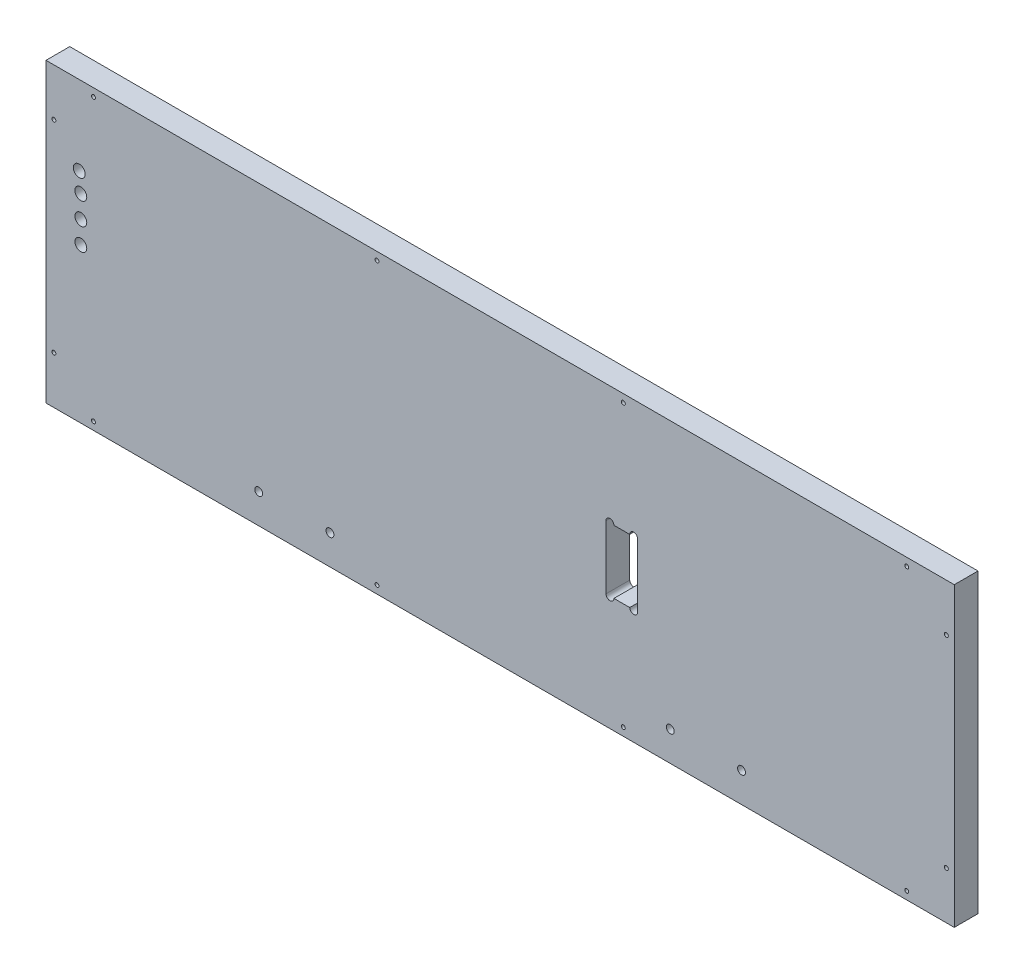
SolidWorks part; units mm, degrees
material "Pine"
ref_plane "Front Plane" through (0, 0, 0) normal (0, 0, 1) x (1, 0, 0)
ref_plane "Top Plane" through (0, 0, 0) normal (0, 1, 0) x (1, 0, 0)
ref_plane "Right Plane" through (0, 0, 0) normal (1, 0, 0) x (0, 0, -1)
sketch "Sketch1" plane through (0, 0, 0) normal (0, 0, 1) x (1, 0, 0)
  line L0 (-5300.6625, 1520.825) -> (-5451.475, 1520.825)
  line L1 (-5456.2375, 1384.3) -> (-5456.2375, 1516.0625)
  line L2 (-5557.8375, 1546.225) -> (-5194.3, 1546.225)
  line L3 (-5557.8375, 1539.875) -> (-5194.3, 1539.875)
  line L4 (-5297.4875, 1377.95) -> (-5454.65, 1377.95)
  line L5 (-5291.1375, 1384.3) -> (-5291.1375, 1516.0625)
  line L6 (-5300.6625, 1525.5875) -> (-5451.475, 1525.5875)
  line L7 (-5461, 1384.3) -> (-5461, 1516.0625)
  line L8 (-5297.4875, 1382.7125) -> (-5454.65, 1382.7125)
  line L9 (-5295.9, 1384.3) -> (-5295.9, 1516.0625)
  line L10 (-5740.4, 998.5375) -> (-5740.4, 1181.1)
  line L11 (-5740.4, 1181.1) -> (-5512.5938, 1181.1)
  line L12 (-5512.5938, 1181.1) -> (-5512.5938, 998.5375)
  line L13 (-5512.5938, 998.5375) -> (-5740.4, 998.5375)
  line L14 (-5258.5938, 1181.1) -> (-5486.4, 1181.1)
  line L15 (-5258.5938, 998.5375) -> (-5258.5938, 1181.1)
  line L16 (-5486.4, 998.5375) -> (-5258.5938, 998.5375)
  line L17 (-5486.4, 1181.1) -> (-5486.4, 998.5375)
  line L18 (-5740.4, 898.525) -> (-5011.7375, 898.525)
  line L19 (-5168.1062, 1384.3) -> (-5168.1062, 1392.2375)
  line L20 (-5176.0437, 1400.175) -> (-5245.8937, 1400.175)
  line L21 (-5253.8313, 1392.2375) -> (-5253.8313, 1384.3)
  line L22 (-5451.475, 1512.8875) -> (-5451.475, 1384.3)
  line L23 (-5303.8375, 1516.0625) -> (-5448.3, 1516.0625)
  line L24 (-5498.3062, 1384.3) -> (-5451.475, 1384.3)
  line L25 (-5253.8313, 1384.3) -> (-5300.6625, 1384.3)
  line L26 (-5584.0312, 1384.3) -> (-5740.4, 1384.3)
  line L27 (-5564.1875, 1536.7) -> (-5740.4, 1536.7)
  line L28 (-5740.4, 1357.3125) -> (-5740.4, 1206.5)
  line L29 (-5011.7375, 1357.3125) -> (-5740.4, 1357.3125)
  line L30 (-5011.7375, 1206.5) -> (-5011.7375, 1357.3125)
  line L31 (-5740.4, 1206.5) -> (-5011.7375, 1206.5)
  line L32 (-4765.675, 1549.4) -> (-4978.4, 1549.4)
  line L33 (-4765.675, 1397) -> (-4765.675, 1549.4)
  line L34 (-4978.4, 1397) -> (-4765.675, 1397)
  line L35 (-4978.4, 1549.4) -> (-4978.4, 1397)
  line L36 (-4765.675, 1371.6) -> (-4978.4, 1371.6)
  line L37 (-4765.675, 1219.2) -> (-4765.675, 1371.6)
  line L38 (-4978.4, 1219.2) -> (-4765.675, 1219.2)
  line L39 (-4978.4, 1371.6) -> (-4978.4, 1219.2)
  line L40 (-5284.7875, 803.275) -> (-5272.0875, 803.275)
  line L41 (-5187.95, 1536.7) -> (-5011.7375, 1536.7)
  line L42 (-5300.6625, 1384.3) -> (-5300.6625, 1512.8875)
  line L43 (-5740.4, 1536.7) -> (-5740.4, 1384.3)
  line L44 (-5557.8375, 1536.7) -> (-5557.8375, 1549.4)
  line L45 (-5557.8375, 1549.4) -> (-5194.3, 1549.4)
  line L46 (-5194.3, 1549.4) -> (-5194.3, 1536.7)
  line L47 (-5011.7375, 1536.7) -> (-5011.7375, 1384.3)
  line L48 (-5011.7375, 1384.3) -> (-5168.1062, 1384.3)
  line L49 (-5498.3062, 1384.3) -> (-5498.3062, 1392.2375)
  line L50 (-5506.2437, 1400.175) -> (-5576.0938, 1400.175)
  line L51 (-5584.0312, 1392.2375) -> (-5584.0312, 1384.3)
  line L52 (-5740.4, 660.4) -> (-5740.4, 898.525)
  line L53 (-5011.7375, 898.525) -> (-5011.7375, 660.4)
  line L54 (-5011.7375, 660.4) -> (-5740.4, 660.4)
  line L55 (-5291.1375, 803.275) -> (-5291.1375, 752.475)
  line L56 (-5265.7375, 752.475) -> (-5265.7375, 803.275)
  line L57 (-5284.7875, 752.475) -> (-5272.0875, 752.475)
  arc A0 (-5451.475, 1520.825) -> (-5456.2375, 1516.0625) centre (-5451.475, 1516.0625) ccw
  arc A1 (-5461, 1384.3) -> (-5454.65, 1377.95) centre (-5454.65, 1384.3) ccw
  arc A2 (-5297.4875, 1377.95) -> (-5291.1375, 1384.3) centre (-5297.4875, 1384.3) ccw
  circle A3 centre (-5037.9312, 1233.4875) radius 1.5875
  circle A4 centre (-5037.9312, 1328.7375) radius 1.5875
  circle A5 centre (-5714.2063, 1233.4875) radius 1.5875
  circle A6 centre (-5714.2063, 1328.7375) radius 1.5875
  circle A7 centre (-5018.0875, 1333.5) radius 1.5875
  circle A8 centre (-5018.0875, 1231.9) radius 1.5875
  circle A9 centre (-5734.05, 1231.9) radius 1.5875
  circle A10 centre (-5734.05, 1333.5) radius 1.5875
  circle A11 centre (-5734.05, 1511.3) radius 1.5875
  circle A12 centre (-5734.05, 1409.7) radius 1.5875
  circle A13 centre (-5018.0875, 1511.3) radius 1.5875
  circle A14 centre (-5018.0875, 1409.7) radius 1.5875
  arc A15 (-5557.8375, 1546.225) -> (-5557.8375, 1539.875) centre (-5557.8375, 1543.05) ccw
  arc A16 (-5194.3, 1539.875) -> (-5194.3, 1546.225) centre (-5194.3, 1543.05) ccw
  arc A17 (-5291.1375, 1516.0625) -> (-5300.6625, 1525.5875) centre (-5300.6625, 1516.0625) ccw
  arc A18 (-5451.475, 1525.5875) -> (-5461, 1516.0625) centre (-5451.475, 1516.0625) ccw
  arc A19 (-5456.2375, 1384.3) -> (-5454.65, 1382.7125) centre (-5454.65, 1384.3) ccw
  arc A20 (-5297.4875, 1382.7125) -> (-5295.9, 1384.3) centre (-5297.4875, 1384.3) ccw
  arc A21 (-5295.9, 1516.0625) -> (-5300.6625, 1520.825) centre (-5300.6625, 1516.0625) ccw
  circle A22 centre (-5702.3, 892.175) radius 1.5875
  circle A23 centre (-5734.05, 860.425) radius 1.5875
  circle A24 centre (-5474.8906, 892.175) radius 1.5875
  circle A25 centre (-5277.2469, 892.175) radius 1.5875
  circle A26 centre (-5049.8375, 892.175) radius 1.5875
  circle A27 centre (-5018.0875, 860.425) radius 1.5875
  circle A28 centre (-5296.6938, 1174.75) radius 1.5875
  circle A29 centre (-5448.3, 1174.75) radius 1.5875
  circle A30 centre (-5264.9437, 1155.7) radius 1.5875
  circle A31 centre (-5264.9437, 1023.9375) radius 1.5875
  circle A32 centre (-5518.9438, 1155.7) radius 1.5875
  circle A33 centre (-5518.9438, 1023.9375) radius 1.5875
  circle A34 centre (-5702.3, 1004.8875) radius 1.5875
  circle A35 centre (-5550.6937, 1004.8875) radius 1.5875
  arc A36 (-5576.0938, 1400.175) -> (-5584.0312, 1392.2375) centre (-5576.0938, 1392.2375) ccw
  arc A37 (-5168.1062, 1392.2375) -> (-5176.0437, 1400.175) centre (-5176.0437, 1392.2375) ccw
  arc A38 (-5245.8937, 1400.175) -> (-5253.8313, 1392.2375) centre (-5245.8937, 1392.2375) ccw
  arc A39 (-5448.3, 1516.0625) -> (-5451.475, 1512.8875) centre (-5448.3, 1512.8875) ccw
  arc A40 (-5284.7875, 803.275) -> (-5291.1375, 803.275) centre (-5287.9625, 803.275) ccw
  circle A41 centre (-5679.2812, 1026.3187) radius 1.5875
  circle A42 centre (-5679.2812, 1153.3187) radius 1.5875
  circle A43 centre (-5571.3313, 1153.3187) radius 1.5875
  circle A44 centre (-5571.3313, 1026.3187) radius 1.5875
  circle A45 centre (-5317.3312, 1153.3187) radius 1.5875
  circle A46 centre (-5317.3312, 1026.3187) radius 1.5875
  circle A47 centre (-5425.2812, 1026.3187) radius 1.5875
  circle A48 centre (-5425.2812, 1153.3187) radius 1.5875
  arc A49 (-5194.3, 1536.7) -> (-5187.95, 1536.7) centre (-5191.125, 1536.7) ccw
  arc A50 (-5564.1875, 1536.7) -> (-5557.8375, 1536.7) centre (-5561.0125, 1536.7) ccw
  arc A51 (-5300.6625, 1512.8875) -> (-5303.8375, 1516.0625) centre (-5303.8375, 1512.8875) ccw
  arc A52 (-5498.3062, 1392.2375) -> (-5506.2437, 1400.175) centre (-5506.2437, 1392.2375) ccw
  circle A53 centre (-5712.46, 784.225) radius 4.7625
  arc A54 (-5272.0875, 752.475) -> (-5265.7375, 752.475) centre (-5268.9125, 752.475) ccw
  arc A55 (-5291.1375, 752.475) -> (-5284.7875, 752.475) centre (-5287.9625, 752.475) ccw
  circle A56 centre (-5182.3938, 684.2125) radius 3.175
  circle A57 centre (-5239.5437, 684.2125) radius 3.175
  circle A58 centre (-5512.5938, 684.2125) radius 3.175
  circle A59 centre (-5569.7437, 684.2125) radius 3.175
  circle A60 centre (-5474.8906, 666.75) radius 1.5875
  circle A61 centre (-5277.2469, 666.75) radius 1.5875
  circle A62 centre (-5734.05, 698.5) radius 1.5875
  circle A63 centre (-5702.3, 666.75) radius 1.5875
  circle A64 centre (-5049.8375, 666.75) radius 1.5875
  circle A65 centre (-5018.0875, 698.5) radius 1.5875
  circle A66 centre (-5713.73, 835.025) radius 4.7625
  circle A67 centre (-5712.46, 819.785) radius 4.7625
  circle A68 centre (-5712.46, 802.005) radius 4.7625
  circle A69 centre (-5714.2063, 1314.45) radius 3.175
  circle A70 centre (-5037.9312, 1314.45) radius 3.175
  arc A71 (-5265.7375, 803.275) -> (-5272.0875, 803.275) centre (-5268.9125, 803.275) ccw
  ellipse E0 centre (-5371.3062, 1089.8188) end of major axis (-5277.6438, 1089.8188) minor radius 65.0875
  ellipse E1 centre (-5625.3062, 1089.8188) end of major axis (-5531.6438, 1089.8188) minor radius 65.0875
sketch "Sketch2" plane through (0, 0, 0) normal (0, 0, 1) x (1, 0, 0)
  line L0 (-5011.7375, 660.4) -> (-5011.7375, 898.525)
  line L1 (-5011.7375, 898.525) -> (-5740.4, 898.525)
  line L2 (-5740.4, 898.525) -> (-5740.4, 660.4)
  line L3 (-5740.4, 660.4) -> (-5011.7375, 660.4)
extrude "Extrude1" add sketch "Sketch2" against normal blind 19.05
sketch "Sketch3" plane through (0, 0, 0) normal (0, 0, 1) x (1, 0, 0)
  line L0 (-5291.1375, 803.275) -> (-5291.1375, 752.475)
  line L1 (-5265.7375, 803.275) -> (-5265.7375, 752.475)
  line L2 (-5284.7875, 803.275) -> (-5272.0875, 803.275)
  line L3 (-5284.7875, 752.475) -> (-5272.0875, 752.475)
  circle A0 centre (-5702.3, 892.175) radius 1.5875
  circle A1 centre (-5734.05, 860.425) radius 1.5875
  circle A2 centre (-5713.73, 835.025) radius 4.7625
  circle A3 centre (-5712.46, 819.785) radius 4.7625
  circle A4 centre (-5712.46, 802.005) radius 4.7625
  circle A5 centre (-5712.46, 784.225) radius 4.7625
  circle A6 centre (-5734.05, 698.5) radius 1.5875
  circle A7 centre (-5702.3, 666.75) radius 1.5875
  circle A8 centre (-5569.7437, 684.2125) radius 3.175
  circle A9 centre (-5512.5938, 684.2125) radius 3.175
  circle A10 centre (-5474.8906, 666.75) radius 1.5875
  circle A11 centre (-5277.2469, 666.75) radius 1.5875
  circle A12 centre (-5239.5437, 684.2125) radius 3.175
  circle A13 centre (-5182.3938, 684.2125) radius 3.175
  circle A14 centre (-5049.8375, 666.75) radius 1.5875
  circle A15 centre (-5018.0875, 698.5) radius 1.5875
  circle A16 centre (-5018.0875, 860.425) radius 1.5875
  circle A17 centre (-5049.8375, 892.175) radius 1.5875
  circle A18 centre (-5277.2469, 892.175) radius 1.5875
  circle A19 centre (-5474.8906, 892.175) radius 1.5875
  arc A20 (-5291.1375, 803.275) -> (-5284.7875, 803.275) centre (-5287.9625, 803.275) cw
  arc A21 (-5272.0875, 803.275) -> (-5265.7375, 803.275) centre (-5268.9125, 803.275) cw
  arc A22 (-5272.0875, 752.475) -> (-5265.7375, 752.475) centre (-5268.9125, 752.475) ccw
  arc A23 (-5284.7875, 752.475) -> (-5291.1375, 752.475) centre (-5287.9625, 752.475) cw
extrude "Cut-Extrude1" cut sketch "Sketch3" against normal up to surface (19.05 mm away) up to face at (-5376.0688, 779.4625, -19.05)
sketch "Sketch4" plane through (0, 660.4, 0) normal (0, -1, 0) x (1, 0, 0)
  line L0 (-5291.1375, -19.05) -> (-5291.1375, -9.525)
  line L1 (-5740.4, -19.05) -> (-5011.7375, -19.05) construction
  line L2 (-5291.1375, -150.8125) -> (-5291.1375, -19.05) construction
  line L3 (-5291.1375, -9.525) -> (-5461, -9.525)
  line L4 (-5461, -9.525) -> (-5461, -19.05)
  line L5 (-5461, -19.05) -> (-5461, -150.8125) construction
  line L6 (-5461, -19.05) -> (-5291.1375, -19.05)
extrude "Cut-Extrude2" cut sketch "Sketch4" against normal blind 3.175
